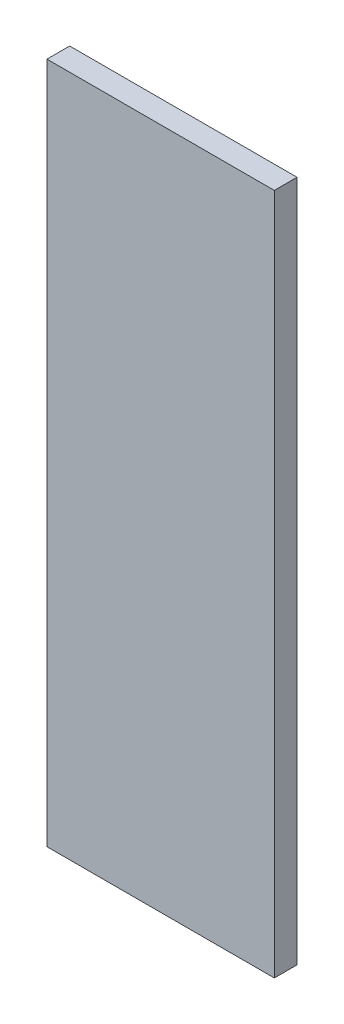
SolidWorks part; units mm, degrees
ref_plane "Front Plane" through (0, 0, 0) normal (0, 0, 1) x (1, 0, 0)
ref_plane "Top Plane" through (0, 0, 0) normal (0, 1, 0) x (1, 0, 0)
ref_plane "Right Plane" through (0, 0, 0) normal (1, 0, 0) x (0, 0, -1)
sketch "Sketch1" plane through (0, 0, 0) normal (0, 0, 1) x (1, 0, 0)
  line L1 (-31.75, 95.25) -> (31.75, 95.25)
  line L2 (-31.75, 95.25) -> (-31.75, -95.25)
  line L3 (-31.75, -95.25) -> (31.75, -95.25)
  line L4 (31.75, 95.25) -> (31.75, -95.25)
  line L5 (-31.75, 95.25) -> (31.75, -95.25) construction
  line L6 (-31.75, -95.25) -> (31.75, 95.25) construction
  point P0 (0, 0)
  dimension "D1" = 63.5
  dimension "D2" = 190.5
extrude "Boss-Extrude1" add sketch "Sketch1" along normal blind 6.35
